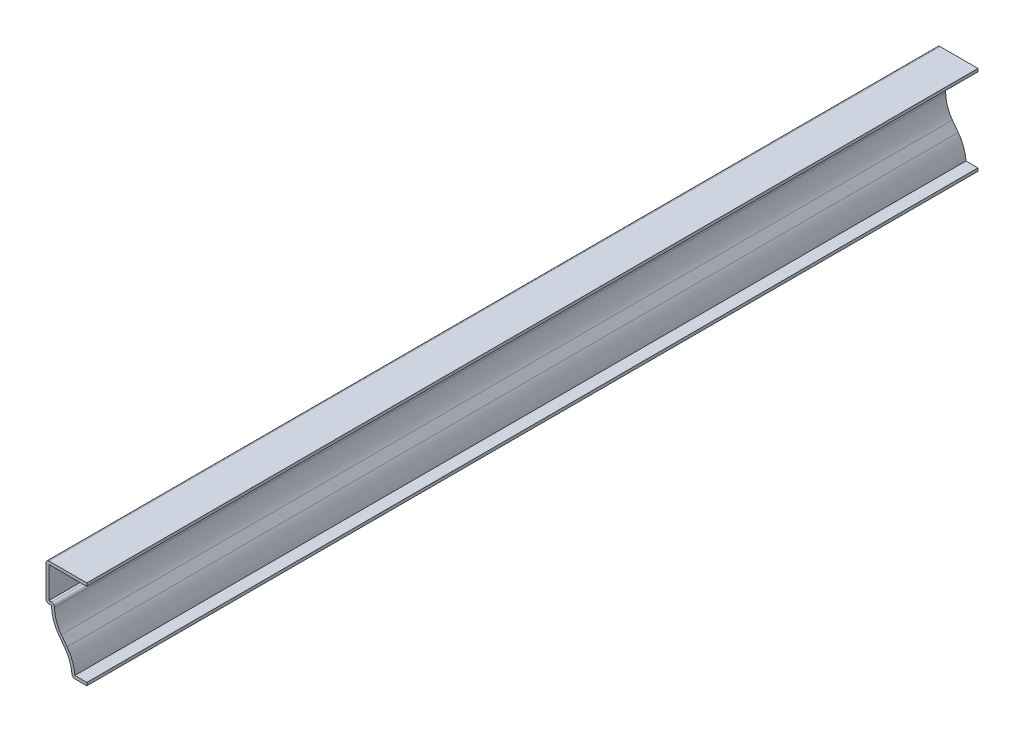
SolidWorks part; units mm, degrees
ref_plane "Front Plane" through (0, 0, 0) normal (0, 0, 1) x (1, 0, 0)
ref_plane "Top Plane" through (0, 0, 0) normal (0, 1, 0) x (1, 0, 0)
ref_plane "Right Plane" through (0, 0, 0) normal (1, 0, 0) x (0, 0, -1)
sketch "Sketch1" plane through (0, 0, 0) normal (0, 0, 1) x (1, 0, 0)
  line L0 (0, 0) -> (-6.35, 0)
  line L1 (-15.0812, 22.225) -> (-17.4625, 22.225)
  line L2 (-17.4625, 22.225) -> (-17.4625, 38.1)
  line L3 (-17.4625, 38.1) -> (0, 38.1)
  line L4 (-15.0812, 22.225) -> (-6.35, 0) construction
  line L5 (-11.9594, 12.7869) -> (-9.4718, 9.4381)
  arc A0 (-15.0812, 22.225) -> (-11.9594, 12.7869) centre (0.7465, 22.225) ccw
  arc A1 (-6.35, 0) -> (-9.4718, 9.4381) centre (-22.1777, 0) ccw
  point P11 (-12.3838, 13.5393)
  point P12 (-11.9594, 12.7869)
  point P13 (0, 0)
  point P14 (-10.7156, 11.1125)
  point P15 (0, 0)
  point P16 (0, 0)
  point P17 (0, 0)
  point P18 (0, 0)
  point P19 (0, 0)
  point P20 (0, 0)
  dimension "D7" = 15.8277
  dimension "D1" = 17.4625
  dimension "D2" = 17.4625
  dimension "D3" = 2.3813
  dimension "D4" = 6.35
  dimension "D5" = 22.225
  dimension "D6" = 38.1
extrude "Extrude-Thin1" add sketch "Sketch1" against normal blind 381 thin
fillet "Fillet1" radius 1.27 4 edges at (-17.4625, 38.1, -190.5) (-17.4625, 22.225, -190.5) (-6.35, 0, -190.5) (-13.7557, 23.495, -190.5)
